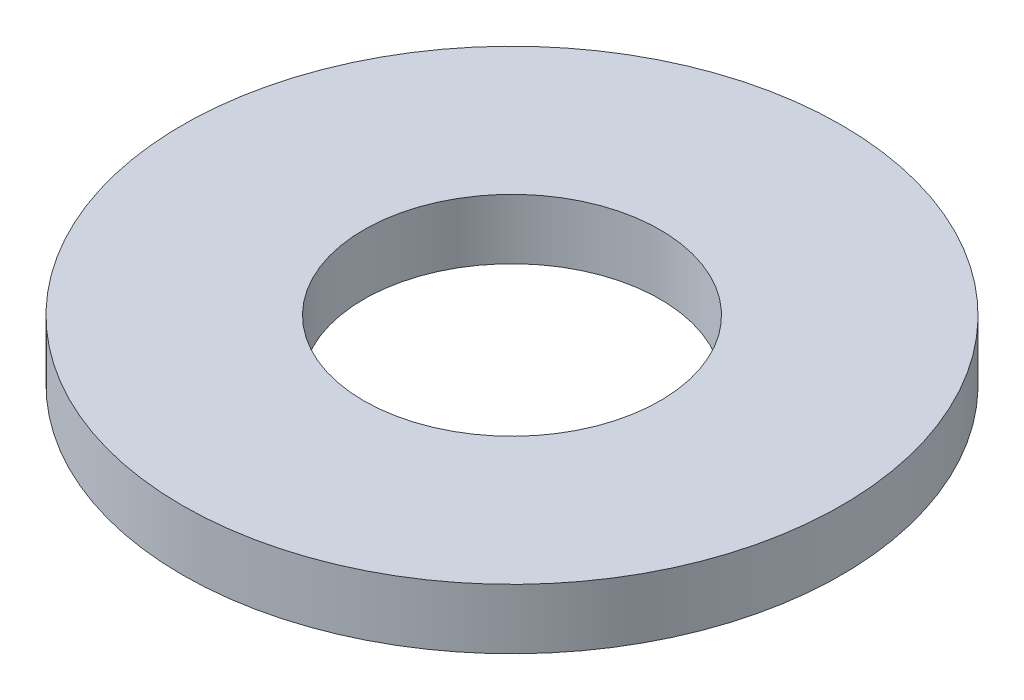
SolidWorks part; units mm, degrees
ref_plane "Front Plane" through (0, 0, 0) normal (0, 0, 1) x (1, 0, 0)
ref_plane "Top Plane" through (0, 0, 0) normal (0, 1, 0) x (1, 0, 0)
ref_plane "Right Plane" through (0, 0, 0) normal (1, 0, 0) x (0, 0, -1)
sketch "Sketch1" plane through (0, 0, 0) normal (0, 1, 0) x (1, 0, 0)
  circle A0 centre (0, 0) radius 7.9375
  dimension "OD" = 15.875
extrude "Boss-Extrude1" add sketch "Sketch1" along normal blind 1.4478
sketch "Sketch5" plane through (0, 1.4478, 0) normal (0, 1, 0) x (-1, 0, 0)
  circle A0 centre (0, 0) radius 3.5687
  dimension "ID" = 7.1374
extrude "Cut-Extrude1" cut sketch "Sketch5" against normal through all
